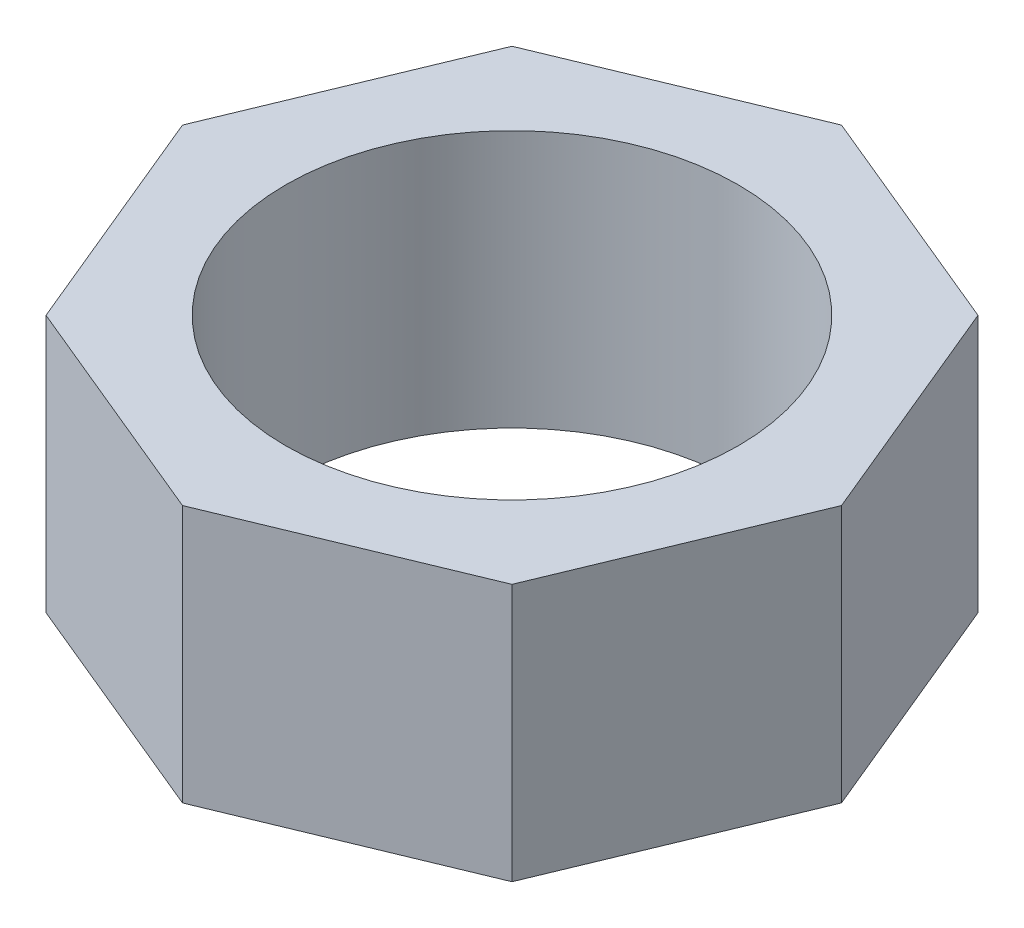
SolidWorks part; units mm, degrees
ref_plane "Front Plane" through (0, 0, 0) normal (0, 0, 1) x (1, 0, 0)
ref_plane "Top Plane" through (0, 0, 0) normal (0, 1, 0) x (1, 0, 0)
ref_plane "Right Plane" through (0, 0, 0) normal (1, 0, 0) x (0, 0, -1)
sketch "Sketch1" plane through (0, 0, 0) normal (0, 1, 0) x (1, 0, 0)
  line L0 (0, -57.9026) -> (43.4223, -39.9165)
  line L1 (61.4085, 3.5058) -> (43.4223, 46.9282)
  line L2 (43.4223, 46.9282) -> (0, 64.9143)
  line L3 (0, 64.9143) -> (-43.4223, 46.9282)
  line L4 (-43.4223, 46.9282) -> (-61.4085, 3.5058)
  line L5 (-61.4085, 3.5058) -> (-43.4223, -39.9165)
  line L6 (-43.4223, -39.9165) -> (0, -57.9026)
  line L7 (43.4223, -39.9165) -> (61.4085, 3.5058)
  circle A0 centre (0, 3.5058) radius 56.734 construction
  circle A1 centre (0, 3.5058) radius 42.15
  dimension "D1" = 47
extrude "Boss-Extrude2" add sketch "Sketch1" along normal blind 48
